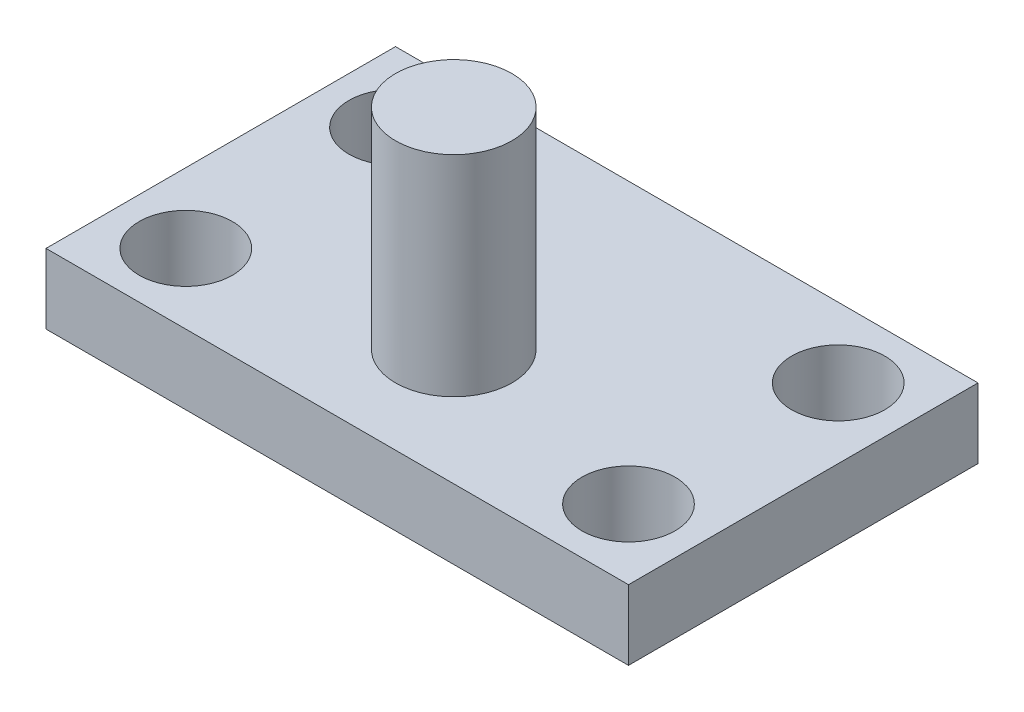
SolidWorks part; units mm, degrees
ref_plane "Front Plane" through (0, 0, 0) normal (0, 0, 1) x (1, 0, 0)
ref_plane "Top Plane" through (0, 0, 0) normal (0, 1, 0) x (1, 0, 0)
ref_plane "Right Plane" through (0, 0, 0) normal (1, 0, 0) x (0, 0, -1)
sketch "Sketch1" plane through (0, 0, 0) normal (0, 1, 0) x (1, 0, 0)
  line L1 (-86.5181, -91.4535) -> (163.4819, -91.4535)
  line L2 (-86.5181, -91.4535) -> (-86.5181, 58.5465)
  line L3 (-86.5181, 58.5465) -> (163.4819, 58.5465)
  line L4 (163.4819, -91.4535) -> (163.4819, 58.5465)
  circle A0 centre (-56.5181, 28.5465) radius 20
  circle A1 centre (133.4819, 28.5465) radius 20
  circle A2 centre (133.4819, -61.4535) radius 20
  circle A3 centre (-56.5181, -61.4535) radius 20
  circle A4 centre (38.4819, -41.4535) radius 25
  point P0 (0, 0)
  dimension "D3" = 150
  dimension "D1" = 30
  dimension "D2" = 30
  dimension "D4" = 250
  dimension "D7" = 125
  dimension "D8" = 50
  dimension "D5" = 2
  dimension "D6" = 2
extrude "Boss-Extrude1" add sketch "Sketch1" along normal mid plane 30
sketch "Sketch2" plane through (0, -15, 0) normal (0, -1, 0) x (1, 0, 0)
  circle A0 centre (38.4819, 41.4535) radius 25
extrude "Boss-Extrude2" add sketch "Sketch2" along normal blind 2 and the other way blind 120
sketch "Sketch3" plane through (0, -17, 0) normal (0, -1, 0) x (-1, 0, 0)
  circle A0 centre (-38.4819, -41.4535) radius 25
extrude "Cut-Extrude1" cut sketch "Sketch3" against normal blind 2
